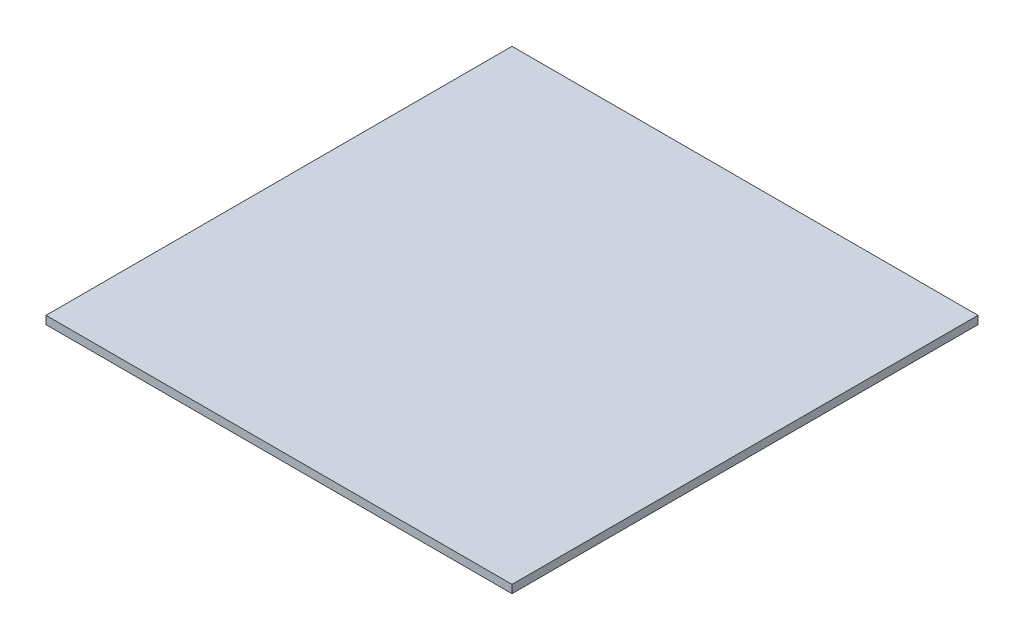
SolidWorks part; units mm, degrees
ref_plane "前视基准面" through (0, 0, 0) normal (0, 0, 1) x (1, 0, 0)
ref_plane "上视基准面" through (0, 0, 0) normal (0, 1, 0) x (1, 0, 0)
ref_plane "右视基准面" through (0, 0, 0) normal (1, 0, 0) x (0, 0, -1)
sketch "草图1" plane through (0, 0, 0) normal (0, 1, 0) x (1, 0, 0)
  line L1 (0, 0) -> (103.6, 0)
  line L2 (0, 0) -> (0, 103.6)
  line L3 (0, 103.6) -> (103.6, 103.6)
  line L4 (103.6, 0) -> (103.6, 103.6)
  dimension "D1" = 103.6
  dimension "D2" = 103.6
extrude "凸台-拉伸1" add sketch "草图1" along normal blind 1.8
